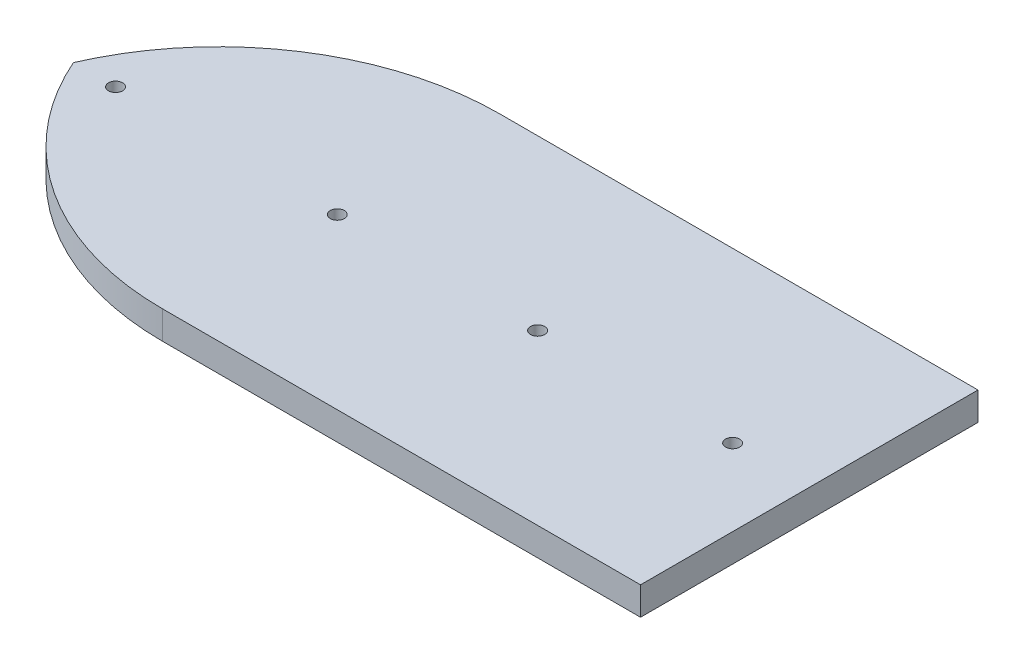
SolidWorks part; units mm, degrees
ref_plane "Front Plane" through (0, 0, 0) normal (0, 0, 1) x (1, 0, 0)
ref_plane "Top Plane" through (0, 0, 0) normal (0, 1, 0) x (1, 0, 0)
ref_plane "Right Plane" through (0, 0, 0) normal (1, 0, 0) x (0, 0, -1)
sketch "Sketch1" plane through (3.6653, -3164.6064, 1.2284) normal (0, 1, 0) x (1, 0, 0)
  line L1 (28.2103, -32.6202) -> (30.2103, -32.6202)
  line L3 (28.2103, -8.6202) -> (-3.7897, -8.6202)
  line L4 (-3.7897, -32.6202) -> (28.2103, -32.6202)
  line L5 (28.2103, -32.6202) -> (28.2103, -8.6202)
  line L6 (28.2103, -8.6202) -> (-3.7897, -8.6202)
  line L7 (-3.7897, -32.6202) -> (28.2103, -32.6202)
  line L15 (28.2103, -8.6202) -> (30.2103, -8.6202)
  line L16 (30.2103, -32.6202) -> (30.2103, -8.6202)
  circle A0 centre (-19.1296, -20.6178) radius 0.5 construction
  circle A1 centre (24.7546, -20.6178) radius 0.5 construction
  arc A2 (-3.7897, -8.6202) -> (-22.12, -20.6202) centre (-3.7897, -28.6202) ccw
  arc A3 (-22.12, -20.6202) -> (-3.7897, -32.6202) centre (-3.7897, -12.6202) ccw
  arc A4 (-3.7897, -8.6202) -> (-22.12, -20.6202) centre (-3.7897, -28.6202) ccw
  arc A5 (-22.12, -20.6202) -> (-3.7897, -32.6202) centre (-3.7897, -12.6202) ccw
  circle A6 centre (10.888, -20.6178) radius 0.5011 construction
  circle A7 centre (-3.3778, -20.5973) radius 0.5 construction
  circle A8 centre (-19.1296, -20.6178) radius 0.5
  circle A9 centre (24.7546, -20.6178) radius 0.5
  circle A10 centre (10.888, -20.6178) radius 0.5011
  circle A11 centre (-3.3778, -20.5973) radius 0.5
  dimension "D2" = 2
  dimension "D1" = 0
extrude "Boss-Extrude1" add sketch "Sketch1" along normal blind 2
